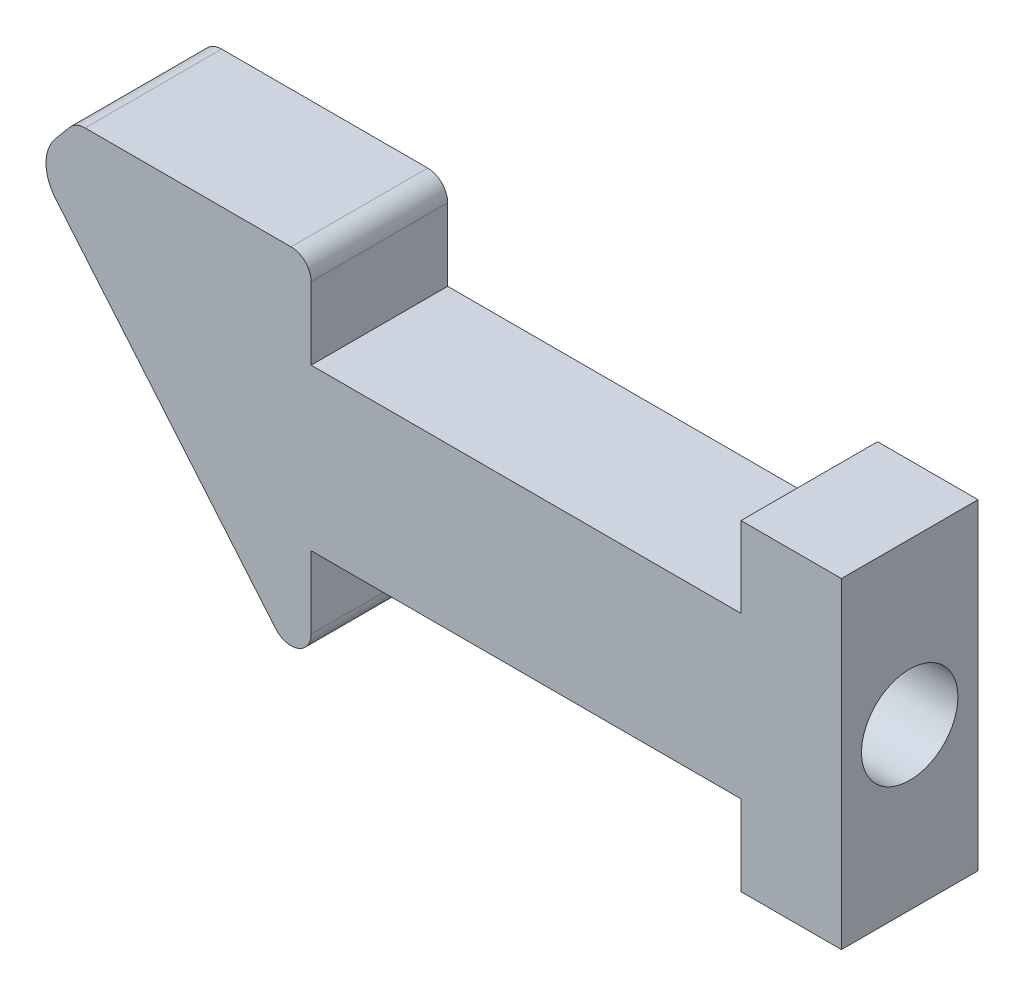
SolidWorks part; units mm, degrees
material "6061 Alloy"
ref_plane "Front Plane" through (0, 0, 0) normal (0, 0, 1) x (1, 0, 0)
ref_plane "Top Plane" through (0, 0, 0) normal (0, 1, 0) x (1, 0, 0)
ref_plane "Right Plane" through (0, 0, 0) normal (1, 0, 0) x (0, 0, -1)
sketch "Sketch2" plane through (0, 0, 0) normal (0, 0, 1) x (1, 0, 0)
  line L1 (-18.8283, 4.3) -> (-13.7, 4.3)
  line L2 (1.87, 0) -> (-1.87, 0) construction
  line L6 (-19.566, 2.413) -> (-14.083, -4.1214)
  line L8 (-13.2, -3.8) -> (-13.2, -2)
  line L11 (-2.5, 2) -> (-2.5, 4)
  line L12 (-2.5, 4) -> (0, 4)
  line L13 (0, 4) -> (0, -4)
  line L14 (0, -4) -> (-2.5, -4)
  line L15 (-2.5, -4) -> (-2.5, -2)
  line L16 (-13.2, 2) -> (-2.5, 2)
  line L17 (-13.2, -2) -> (-2.5, -2)
  line L18 (-19.566, 3.6986) -> (-19.2113, 4.1214)
  line L19 (-13.2, 2) -> (-13.2, 3.8)
  arc A1 (-14.083, -4.1214) -> (-13.2, -3.8) centre (-13.7, -3.8) ccw
  arc A3 (-19.566, 2.413) -> (-19.566, 3.6986) centre (-18.8, 3.0558) cw
  arc A4 (-18.8283, 4.3) -> (-19.2113, 4.1214) centre (-18.8283, 3.8) ccw
  arc A7 (-13.2, 3.8) -> (-13.7, 4.3) centre (-13.7, 3.8) ccw
  point P1 (-13.2, 3.7)
  point P3 (-13.7, -4.582)
  point P6 (-13.272, 3.7)
  point P9 (0, 0)
  point P20 (-13.2, -5.1737)
  point P21 (-13.7, -4.9082)
  point P22 (-13.7, -6.16)
  dimension "D1" = 1
  dimension "D9" = 4.3
  dimension "D4" = 0.5
  dimension "D12" = 0.5
  dimension "D6" = 8.1
  dimension "D5" = 0.5
  dimension "D2" = 2.5
  dimension "D3" = 13.2
  dimension "D7" = 8
  dimension "D8" = 4
  dimension "D11" = 5.1
  dimension "D13" = 40
  dimension "D14" = 40
extrude "Boss-Extrude3" add sketch "Sketch2" along normal mid plane 3.4
sketch "Sketch3" plane through (0, 0, 0) normal (1, 0, 0) x (0, 0, -1)
  line L0 (-1.7, 4) -> (1.7, 4) construction
  circle A0 centre (0, 0) radius 0.95
  point P7 (0, 4)
  dimension "D1" = 1.9
  dimension "D2" = 2
extrude "Cut-Extrude1" cut sketch "Sketch3" against normal blind 9.5
sketch "Sketch4" plane through (0, 0, 0) normal (1, 0, 0) x (0, 0, -1)
  circle A0 centre (0, 0) radius 1.2
  point P3 (0, 0)
  dimension "D1" = 2.4
extrude "Cut-Extrude2" cut sketch "Sketch4" against normal blind 2.8
